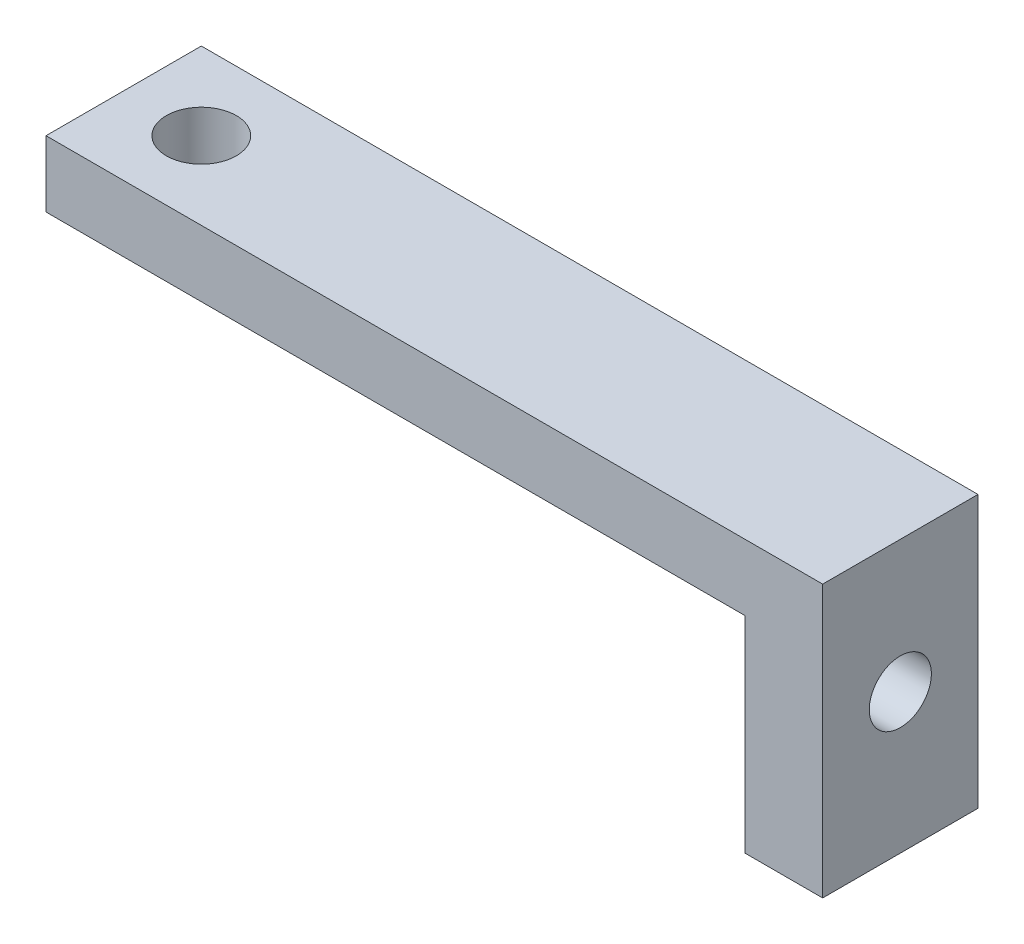
SolidWorks part; units mm, degrees
ref_plane "Front Plane" through (0, 0, 0) normal (0, 0, 1) x (1, 0, 0)
ref_plane "Top Plane" through (0, 0, 0) normal (0, 1, 0) x (1, 0, 0)
ref_plane "Right Plane" through (0, 0, 0) normal (1, 0, 0) x (0, 0, -1)
sketch "Sketch1" plane through (0, 0, 0) normal (0, 0, 1) x (1, 0, 0)
  line L0 (-75.9211, -12.5721) -> (-75.9211, -10.4102)
  line L1 (-75.9211, -10.4102) -> (-50.5211, -10.4102)
  line L2 (-50.5211, -10.4102) -> (-50.5211, -19.3002)
  line L3 (-50.5211, -19.3002) -> (-53.0611, -19.3002)
  line L4 (-53.0611, -19.3002) -> (-53.0611, -12.5721)
  line L5 (-53.0611, -12.5721) -> (-75.9211, -12.5721)
  dimension "D1" = 25.4
  dimension "D2" = 2.54
  dimension "D3" = 8.89
extrude "Boss-Extrude1" add sketch "Sketch1" along normal blind 5.08 contours L4 L5 L0 L1 L2 L3
sketch "Sketch2" plane through (0, -10.4102, 0) normal (0, 1, 0) x (1, 0, 0)
  line L0 (-75.9211, -5.08) -> (-50.5211, -5.08) construction
  line L1 (-75.9211, -5.08) -> (-75.9211, 0) construction
  circle A0 centre (-73.3811, -2.54) radius 1.143
  dimension "D1" = 2.54
  dimension "D2" = 2.54
extrude "Cut-Extrude1" cut sketch "Sketch2" against normal blind 5.08
sketch "Sketch3" plane through (-50.5211, 0, 0) normal (1, 0, 0) x (0, 0, -1)
  line L0 (-5.08, -10.4102) -> (-5.08, -19.3002) construction
  line L2 (-5.08, -19.3002) -> (0, -19.3002) construction
  circle A0 centre (-2.54, -14.7282) radius 1.016
  dimension "D1" = 2.54
  dimension "D2" = 4.572
extrude "Cut-Extrude2" cut sketch "Sketch3" against normal blind 5.08
